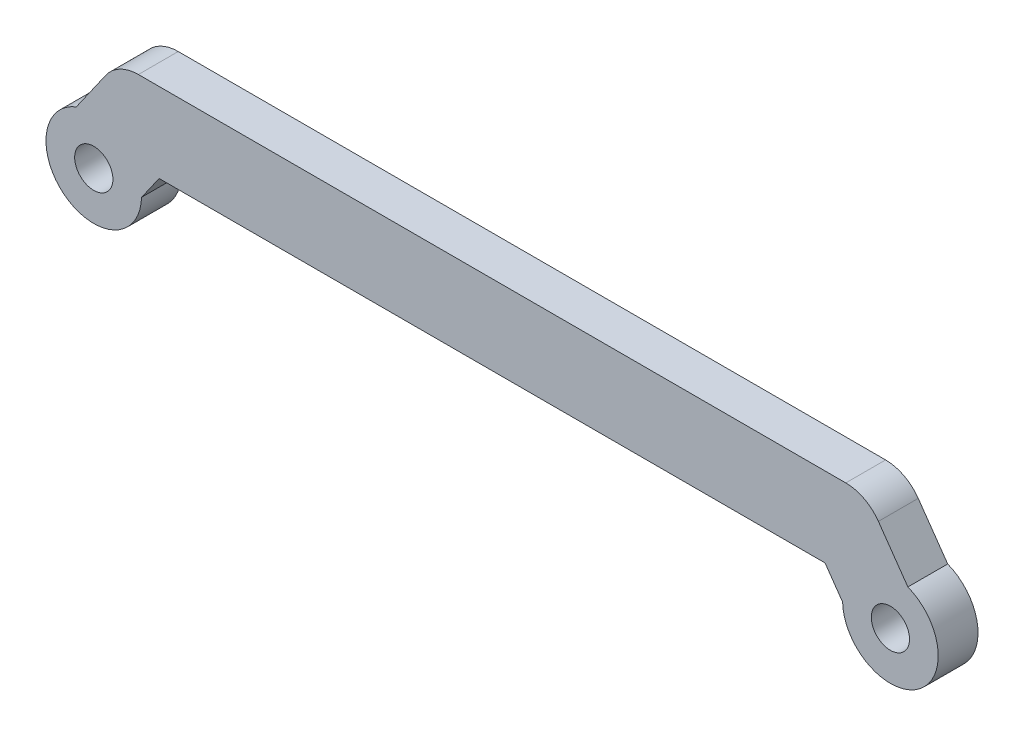
SolidWorks part; units mm, degrees
ref_plane "Front Plane" through (0, 0, 0) normal (0, 0, 1) x (1, 0, 0)
ref_plane "Top Plane" through (0, 0, 0) normal (0, 1, 0) x (1, 0, 0)
ref_plane "Right Plane" through (0, 0, 0) normal (1, 0, 0) x (0, 0, -1)
sketch "Sketch1" plane through (0, 0, 0) normal (0, 0, 1) x (1, 0, 0)
  line L0 (-25, 2.5) -> (25, 2.5)
  line L1 (-25, -2.5) -> (25, -2.5)
  line L2 (-25, 0) -> (25, 0) construction
  line L3 (-25, 0) -> (-22.1992, 4) construction
  line L4 (-22.1992, 4) -> (22.1992, 4) construction
  line L5 (22.1992, 4) -> (25, 0) construction
  line L6 (-25, 0) -> (-22.1992, 4) construction
  line L7 (-27.0479, 1.4339) -> (-24.247, 5.4339)
  line L8 (-22.9521, -1.4339) -> (-20.1513, 2.5661)
  line L9 (25, 0) -> (22.1992, 4) construction
  line L10 (22.9521, -1.4339) -> (20.1513, 2.5661)
  line L11 (27.0479, 1.4339) -> (24.247, 5.4339)
  line L12 (22.1992, 4) -> (-22.1992, 4) construction
  line L13 (22.1992, 1.5) -> (-22.1992, 1.5)
  line L14 (22.1992, 6.5) -> (-22.1992, 6.5)
  circle A0 centre (-25, 0) radius 1.2
  circle A1 centre (-25, 0) radius 2.5
  circle A2 centre (25, 0) radius 1.2
  circle A3 centre (25, 0) radius 2.5
  arc A4 (-27.0479, 1.4339) -> (-22.9521, -1.4339) centre (-25, 0) ccw
  arc A5 (-20.1513, 2.5661) -> (-24.247, 5.4339) centre (-22.1992, 4) ccw
  arc A6 (22.9521, -1.4339) -> (27.0479, 1.4339) centre (25, 0) ccw
  arc A7 (24.247, 5.4339) -> (20.1513, 2.5661) centre (22.1992, 4) ccw
  arc A8 (22.1992, 1.5) -> (22.1992, 6.5) centre (22.1992, 4) ccw
  arc A9 (-22.1992, 6.5) -> (-22.1992, 1.5) centre (-22.1992, 4) ccw
  point P10 (0, 0)
  point P11 (-23.5996, 2)
  point P19 (23.5996, 2)
  point P24 (0, 4)
  point P31 (0, 5)
  point P32 (0, 0)
  dimension "D1" = 2.4
  dimension "D2" = 5
  dimension "D3" = 5
  dimension "D5" = 2.4
  dimension "D4" = 50
  dimension "D6" = 4
  dimension "D7" = 125
extrude "Boss-Extrude1" add sketch "Sketch1" along normal mid plane 2.5 contours A7 L14 A5 L8 L0 L10 | A5 A9 L0 L8 | L0 A8 A7 L10 | A8 L0 A3 L11 | A3 L0 L10 | A3 A2 | A9 L7 A1 L0 | A1 L8 L0 | A1 A0 | A8 A3 L0 | A3 A8 | A8 L13 L10 A3 | L13 L10 L0 L8 | A9 A1 L8 L13 | A9 L0 A1 | A1 A9
sketch "Sketch2" plane through (0, 0, -1.25) normal (0, 0, -1) x (-1, 0, 0)
  circle A0 centre (25, 0) radius 3
  circle A1 centre (25, 0) radius 1.2 construction
  circle A2 centre (25, 0) radius 1.2
  circle A3 centre (-25, 0) radius 3
  circle A4 centre (-25, 0) radius 1.2 construction
  circle A5 centre (-25, 0) radius 1.2
  dimension "D1" = 6
  dimension "D2" = 6
extrude "Boss-Extrude2" add sketch "Sketch2" against normal up to surface (2.5 mm away) up to face at (0, 2.3273, 1.25)
